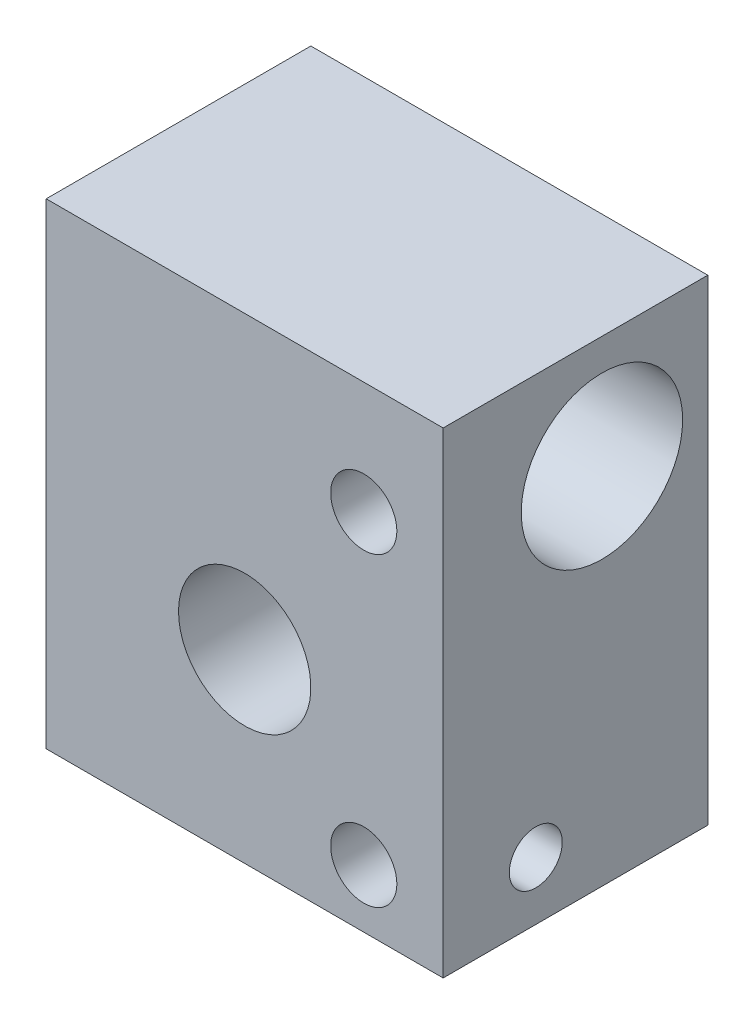
SolidWorks part; units mm, degrees
material "aluminio"
ref_plane "Front Plane" through (0, 0, 0) normal (0, 0, 1) x (1, 0, 0)
ref_plane "Top Plane" through (0, 0, 0) normal (0, 1, 0) x (1, 0, 0)
ref_plane "Right Plane" through (0, 0, 0) normal (1, 0, 0) x (0, 0, -1)
sketch "Sketch1" plane through (0, 0, 0) normal (0, 0, 1) x (1, 0, 0)
  line L1 (-7.5, -9) -> (7.5, -9)
  line L2 (-7.5, -9) -> (-7.5, 9)
  line L3 (-7.5, 9) -> (7.5, 9)
  line L4 (7.5, -9) -> (7.5, 9)
  line L5 (-7.5, -9) -> (7.5, 9) construction
  line L6 (-7.5, 9) -> (7.5, -9) construction
  point P0 (0, 0)
  dimension "D1" = 18
  dimension "D2" = 15
extrude "Boss-Extrude1" add sketch "Sketch1" along normal blind 10
sketch "Sketch2" plane through (0, 0, 0) normal (0, 0, -1) x (-1, 0, 0)
  line L0 (0, 9) -> (0, -9) construction
  line L1 (7.5, -9) -> (-7.5, -9) construction
  line L2 (-7.5, 9) -> (7.5, 9) construction
  circle A0 centre (0, -2) radius 2.5
  dimension "D1" = 5
  dimension "D2" = 7
extrude "Cut-Extrude1" cut sketch "Sketch2" against normal through all
cosmetic thread "Rosca cosmética1" parameters "D2"=6
sketch "Sketch3" plane through (7.5, 0, 0) normal (1, 0, 0) x (0, 0, -1)
  line L0 (-10, 0) -> (0, 0) construction
  line L1 (-10, -9) -> (-10, 9) construction
  line L2 (0, -9) -> (0, 9) construction
  line L3 (-4, 0) -> (-4, 9) construction
  line L5 (-10, 9) -> (0, 9) construction
  circle A0 centre (-4, 4.75) radius 3.05
  dimension "D1" = 6.1
  dimension "D3" = 4
  dimension "D2" = 1.2
extrude "Cut-Extrude2" cut sketch "Sketch3" against normal through all
sketch "Sketch4" plane through (7.5, 0, 0) normal (1, 0, 0) x (0, 0, -1)
  line L0 (0, -6.8) -> (-10, -6.8) construction
  line L3 (-6.5, -6.8) -> (-6.5, -9) construction
  line L4 (-10, -9) -> (0, -9) construction
  line L5 (0, -9) -> (0, 9) construction
  line L6 (-10, -9) -> (-10, 9) construction
  circle A0 centre (-6.5, -6.8) radius 0.9
  dimension "D1" = 1.8
  dimension "D2" = 2.2
  dimension "D3" = 3.5
hole_wizard "Taladro roscado M31" positions "Croquis3" profile "Croquis2" tap size "M3" standard "Iso"
sketch "Croquis3" plane through (-2.6487, -2.9752, 10) normal (0, 0, -1) x (1, 0, 0)
  line L3 (10.1487, -7.7252) -> (-4.8513, -7.7252) construction
  line L4 (10.1487, 6.0248) -> (10.1487, -11.9752) construction
  line L5 (-4.8513, -11.9752) -> (-4.8513, 6.0248) construction
  line L7 (10.1487, -10.7752) -> (10.1487, -4.6752) construction
  line L8 (10.1487, 3.8248) -> (-4.8513, 3.8248) construction
  point P0 (7.1487, -7.7252)
  point P28 (7.1487, 3.8248)
  dimension "D1" = 3
  dimension "D2" = 3
cosmetic thread "Rosca de taladro1" parameters "D1"=3.2179, "D2"=3
cosmetic thread "Rosca de taladro4" parameters "D1"=4, "D2"=3
sketch "Croquis2" plane through (4.5, 4.75, 10) normal (1, 0, 0) x (0, -1, 0)
  line L0 (0, 0) -> (0, 4.7511)
  line L1 (0, 4.7511) -> (1.25, 4)
  line L2 (1.25, 4) -> (1.25, 0)
  line L5 (1.25, 0) -> (0, 0)
  line L10 (0, 4.7511) -> (-1.25, 4) construction
  line L11 (0, -6.35) -> (0, 107.95) construction
  dimension "Diámetro de perforador para roscar" = 2.5
  dimension "Profundidad de perforador para roscar" = 4
  dimension "Ángulo de perforador" = 118
sketch "Croquis8" plane through (0, 0, 10) normal (0, 0, 1) x (1, 0, 0)
  line L1 (7.5, 4.75) -> (-7.5, 4.75) construction
  line L2 (7.5, -9) -> (7.5, 9) construction
  line L3 (-7.5, 9) -> (-7.5, -9) construction
  line L4 (7.5, 1.7) -> (7.5, 7.8) construction
  line L5 (-7.5, 7.8) -> (-7.5, 1.7) construction
  point P0 (0, 4.75)
hole_wizard "Diámetro de taladro Ø2.8 (2.8)1" positions "Croquis3D1" profile "Croquis11" hole size "Ø2.8" standard "Iso"
sketch3d "Croquis3D1"
  point P0 (7.5, -6.8, 6.5)
sketch "Croquis11" plane through (7.5, -6.8, 6.5) normal (0, 1, 0) x (0, 0, -1)
  line L0 (0, 0) -> (0, 12.6009)
  line L1 (0, 12.6009) -> (1, 12)
  line L2 (1, 12) -> (1, 0)
  line L5 (1, 0) -> (0, 0)
  line L10 (0, 12.6009) -> (-1, 12) construction
  line L11 (0, -6.35) -> (0, 107.95) construction
  dimension "Diámetro de taladro" = 2
  dimension "Profundidad de taladro" = 12
  dimension "Ángulo de perforador" = 118
